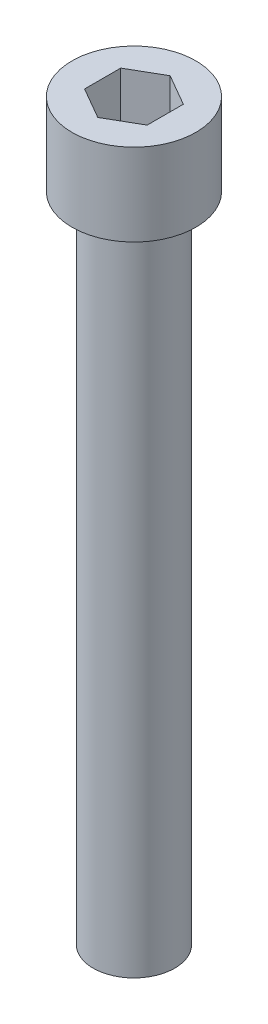
SolidWorks part; units mm, degrees
ref_plane "Front Plane" through (0, 0, 0) normal (0, 0, 1) x (1, 0, 0)
ref_plane "Top Plane" through (0, 0, 0) normal (0, 1, 0) x (1, 0, 0)
ref_plane "Right Plane" through (0, 0, 0) normal (1, 0, 0) x (0, 0, -1)
sketch "Sketch2" plane through (0, 0, 0) normal (0, 1, 0) x (1, 0, 0)
  circle A0 centre (0, 0) radius 4.75
  dimension "D1" = 9.5
extrude "Boss-Extrude1" add sketch "Sketch2" along normal blind 6.3
sketch "Sketch3" plane through (0, 0, 0) normal (0, -1, 0) x (1, 0, 0)
  circle A0 centre (0, 0) radius 3.125
  dimension "D1" = 6.25
extrude "Boss-Extrude2" add sketch "Sketch3" along normal blind 50
sketch "Sketch4" plane through (0, 6.3, 0) normal (0, 1, 0) x (1, 0, 0)
  line L1 (-2.4, 1.3856) -> (-2.4, -1.3856)
  line L2 (-2.4, -1.3856) -> (0, -2.7713)
  line L3 (0, -2.7713) -> (2.4, -1.3856)
  line L4 (2.4, -1.3856) -> (2.4, 1.3856)
  line L5 (2.4, 1.3856) -> (0, 2.7713)
  line L6 (0, 2.7713) -> (-2.4, 1.3856)
  circle A0 centre (0, 0) radius 2.4 construction
  dimension "D1" = 4.8
extrude "Cut-Extrude1" cut sketch "Sketch4" against normal blind 4.25
